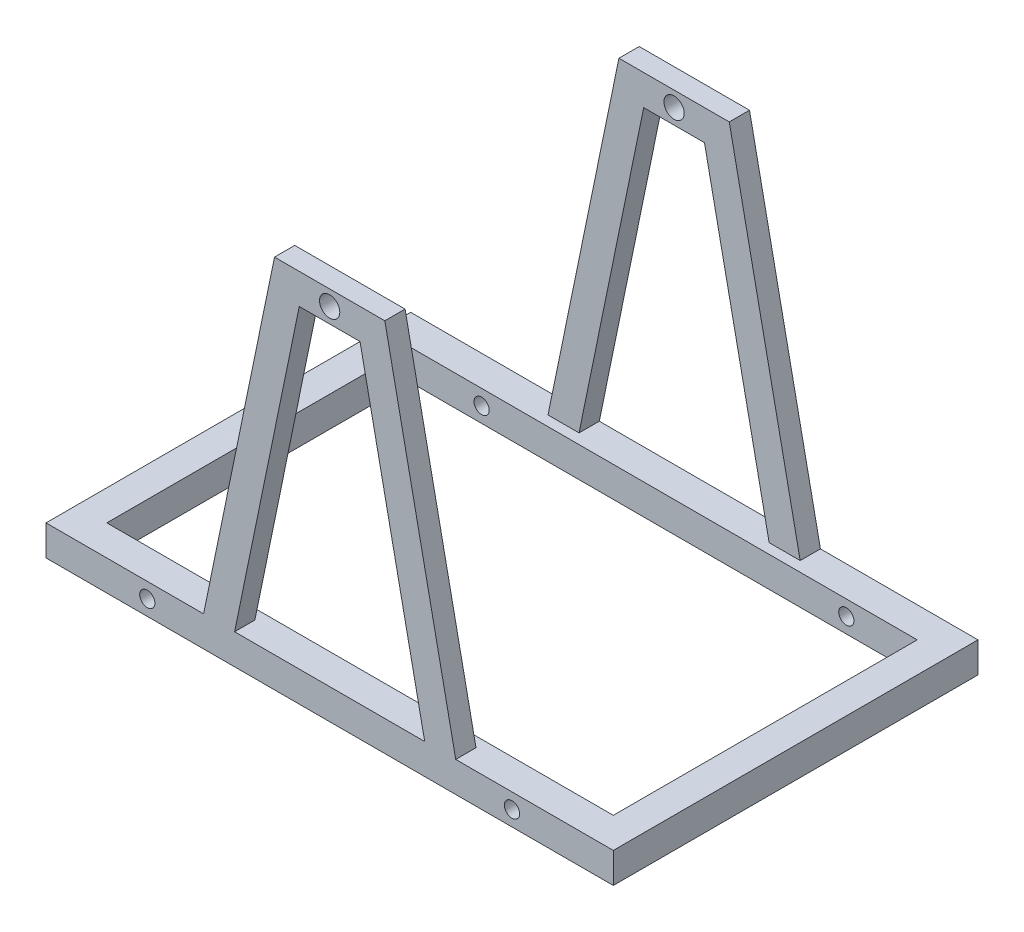
SolidWorks part; units mm, degrees
ref_plane "Front Plane" through (0, 0, 0) normal (0, 0, 1) x (1, 0, 0)
ref_plane "Top Plane" through (0, 0, 0) normal (0, 1, 0) x (1, 0, 0)
ref_plane "Right Plane" through (0, 0, 0) normal (1, 0, 0) x (0, 0, -1)
sketch "Sketch1" plane through (0, 0, 0) normal (0, 1, 0) x (1, 0, 0)
  line L1 (250, 150) -> (-250, 150)
  line L2 (250, 150) -> (250, -150)
  line L3 (250, -150) -> (-250, -150)
  line L4 (-250, 150) -> (-250, -150)
  line L5 (250, 150) -> (-250, -150) construction
  line L6 (250, -150) -> (-250, 150) construction
  point P0 (0, 0)
  dimension "D1" = 500
  dimension "D2" = 300
extrude "Extrude-Thin1" add sketch "Sketch1" along normal blind 30 thin
sketch "Sketch2" plane through (0, 0, 180) normal (0, 0, 1) x (1, 0, 0)
  line L0 (0, 106.226) -> (0, -88.3454) construction
  line L1 (-280, 0) -> (280, 0) construction
  circle A0 centre (-180, 15) radius 7.5
  circle A1 centre (180, 15) radius 7.5
  dimension "D1" = 15
  dimension "D2" = 15
  dimension "D3" = 180
extrude "Cut-Extrude1" cut sketch "Sketch2" against normal through all
sketch "Sketch3" plane through (0, 0, 180) normal (0, 0, 1) x (1, 0, 0)
  line L0 (-100, 0) -> (-30, 340)
  line L1 (-280, 0) -> (280, 0) construction
  line L2 (-30, 340) -> (30, 340)
  line L3 (0, 340) -> (0, 0) construction
  line L4 (100, 0) -> (30, 340)
  dimension "D1" = 30
  dimension "D2" = 100
  dimension "D3" = 340
extrude "Extrude-Thin2" add sketch "Sketch3" against normal blind 20 thin thin type one direction wall 30
sketch "Sketch4" plane through (0, 0, 180) normal (0, 0, 1) x (1, 0, 0)
  circle A0 centre (0, 355) radius 10
  point P5 (26.0782, 185.8942)
  dimension "D1" = 20
  dimension "D2" = 280
  dimension "D3" = 355
extrude "Cut-Extrude2" cut sketch "Sketch4" against normal through all
mirror "Mirror1" about plane through (0, 0, 0) normal (0, 0, 1) of "Cut-Extrude2", "Extrude-Thin2"
